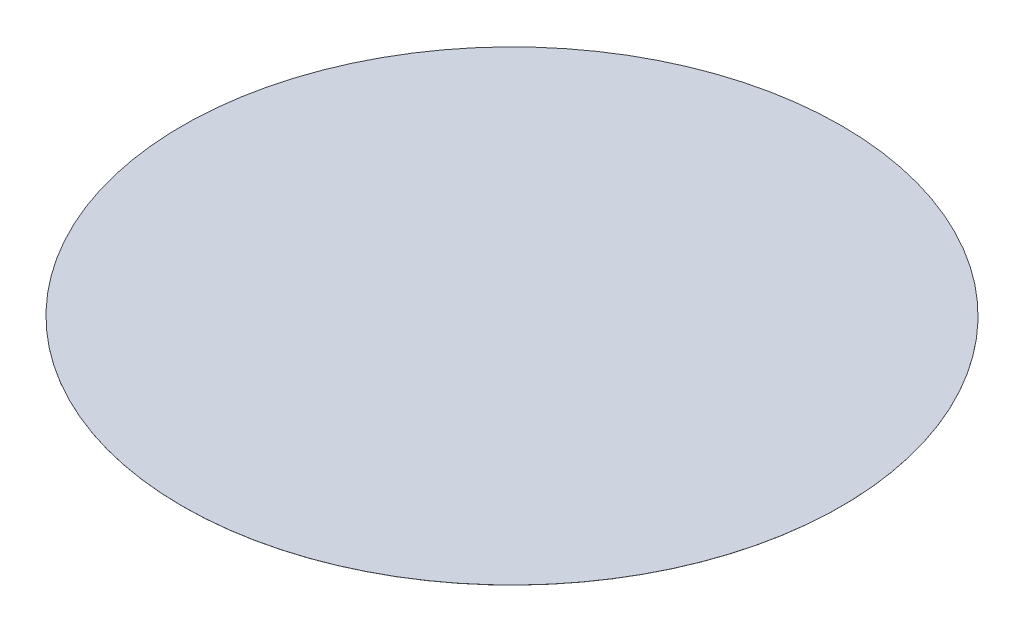
SolidWorks part; units mm, degrees
ref_plane "Front Plane" through (0, 0, 0) normal (0, 0, 1) x (1, 0, 0)
ref_plane "Top Plane" through (0, 0, 0) normal (0, 1, 0) x (1, 0, 0)
ref_plane "Right Plane" through (0, 0, 0) normal (1, 0, 0) x (0, 0, -1)
sketch "Sketch1" plane through (0, 0, 0) normal (0, 1, 0) x (1, 0, 0)
  line L0 (0, 0) -> (973.4794, 612.24)
  line L1 (1016.9551, -536.9379) -> (0, 0)
  arc A0 (1150, 0) -> (973.4794, 612.24) centre (0, 0) ccw
  arc A1 (1150, 0) -> (1016.9551, -536.9379) centre (0, 0) cw
  point P5 (990.7874, -583.8153)
  dimension "D1" = 1150
  dimension "D3" = 973.4794
  dimension "D2" = 60
extrude "Boss-Extrude1" add sketch "Sketch1" along normal blind 0.25
sketch "Sketch12" plane through (0, 0, 0) normal (0, 1, 0) x (1, 0, 0)
  line L1 (1202.5081, 755.2313) -> (1360.4697, 406.8441)
  line L4 (936.6144, 590.3996) -> (1072.1765, 322.7749)
  line L5 (1106.2731, -276.4001) -> (1072.1765, 322.7749)
  line L6 (1016.9187, -537.0069) -> (1106.2731, -276.4001)
  line L7 (936.6144, 590.3996) -> (1202.5081, 755.2313)
  line L8 (1016.9187, -537.0069) -> (1262.6099, -649.7817)
  line L10 (1376.6123, -348.3368) -> (1360.4697, 406.8441)
  line L11 (1262.6099, -649.7817) -> (1376.6123, -348.3368)
  arc A0 (1016.9551, -536.9379) -> (973.4794, 612.24) centre (0, 0) ccw construction
  point P0 (1016.9187, -537.0069)
  dimension "D2" = 1420
  dimension "D3" = 1420
  dimension "D4" = 1420
  dimension "D5" = 300
  dimension "D6" = 56.451
  dimension "D7" = 312.8401
  dimension "D8" = 1420
  dimension "D9" = 936.6144
  dimension "D10" = 1016.9187
  dimension "D11" = 1072.1765
  dimension "D12" = 1106.2731
  dimension "D13" = 1202.5081
  dimension "D14" = 276.4001
  dimension "D15" = 382.5252
  dimension "D17" = 1376.6123
sketch "Sketch19" plane through (0, 0, 0) normal (0, 0, 1) x (1, 0, 0)
  line L1 (0, 28.8009) -> (0, -36.39)
  dimension "D1" = 65.1908
  dimension "D2" = 28.8009
sketch "Sketch20" plane through (0, 0, 0) normal (0, 1, 0) x (1, 0, 0)
  line L0 (0, 0) -> (1722.2089, 0) construction
  circle A0 centre (1200, -350) radius 75
  circle A1 centre (1200, 350) radius 75
  dimension "D5" = 150
  dimension "D6" = 150
  dimension "D1" = 1250
  dimension "D2" = 1250
  dimension "D3" = 350
  dimension "D4" = 700
sketch "Sketch23" plane through (0, 0, 0) normal (0, 0, 1) x (1, 0, 0)
  circle A0 centre (938.7303, 289.9856) radius 2.5
  dimension "D1" = 5
pattern_circular "CirPattern11" count 6 over 360 about axis through (0, 28.8009, 0) along (0, -1, 0) of "Boss-Extrude1"
